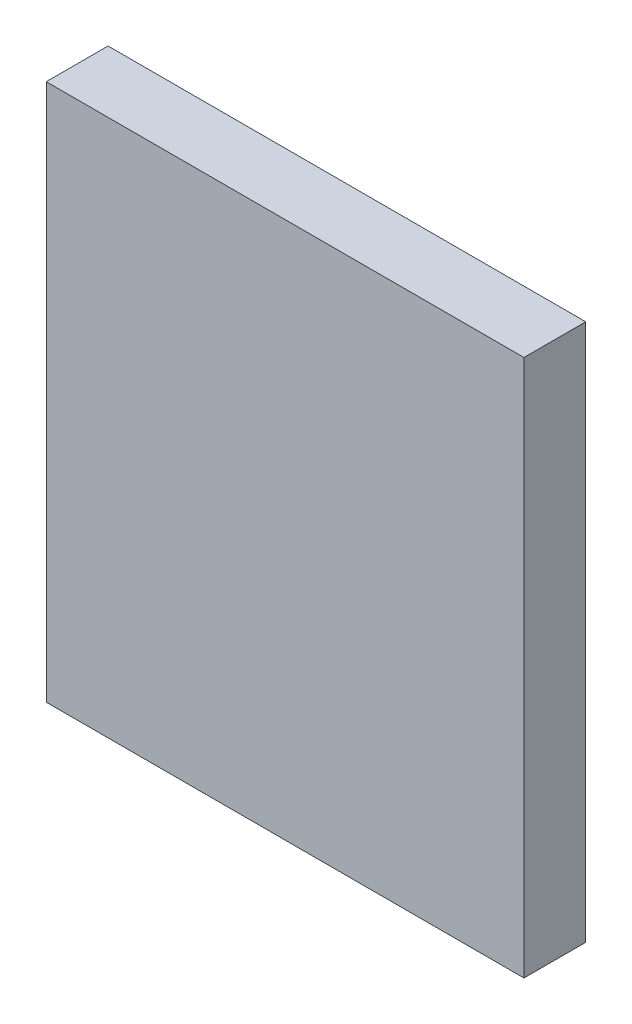
SolidWorks part; units mm, degrees
ref_plane "Front Plane" through (0, 0, 0) normal (0, 0, 1) x (1, 0, 0)
ref_plane "Top Plane" through (0, 0, 0) normal (0, 1, 0) x (1, 0, 0)
ref_plane "Right Plane" through (0, 0, 0) normal (1, 0, 0) x (0, 0, -1)
sketch "Sketch2" plane through (0, 0, 0) normal (0, 0, 1) x (1, 0, 0)
  line L1 (0, 0) -> (136, 0)
  line L2 (0, 0) -> (0, 153)
  line L3 (0, 153) -> (136, 153)
  line L4 (136, 0) -> (136, 153)
  dimension "D1" = 136
  dimension "D2" = 153
extrude "Boss-Extrude1" add sketch "Sketch2" along normal blind 17.6
